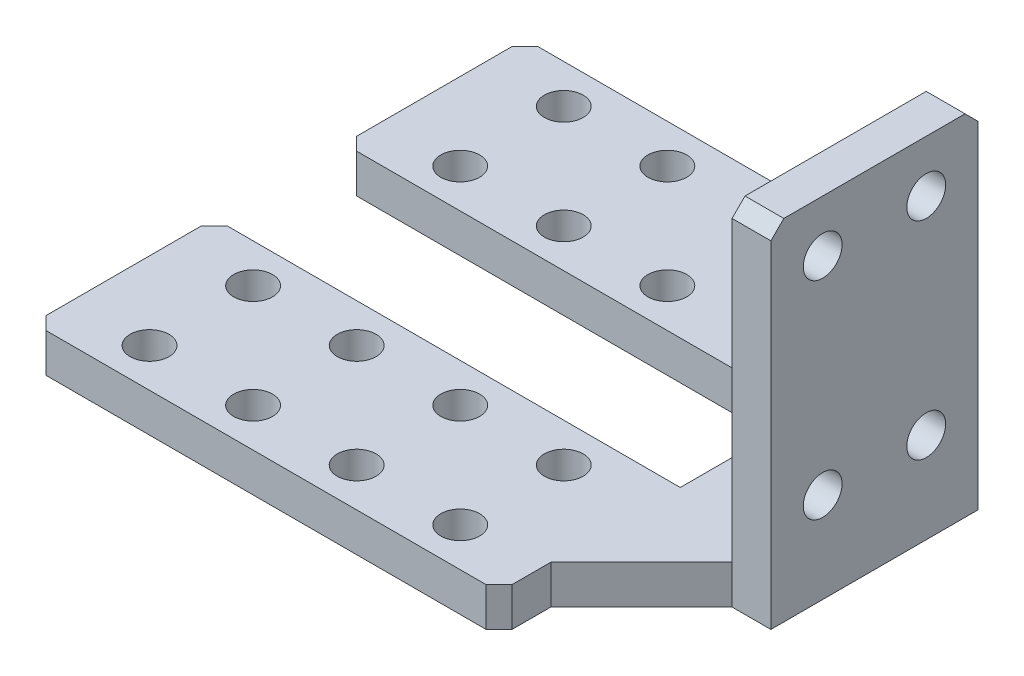
SolidWorks part; units mm, degrees
ref_plane "前视基准面" through (0, 0, 0) normal (0, 0, 1) x (1, 0, 0)
ref_plane "上视基准面" through (0, 0, 0) normal (0, 1, 0) x (1, 0, 0)
ref_plane "右视基准面" through (0, 0, 0) normal (1, 0, 0) x (0, 0, -1)
sketch "草图1" plane through (0, 0, 0) normal (0, 0, 1) x (1, 0, 0)
  line L1 (0, 0) -> (-3, 0)
  line L2 (0, 0) -> (0, 24)
  line L3 (0, 24) -> (-3, 24)
  line L4 (-3, 0) -> (-3, 24)
  dimension "D1" = 3
  dimension "D2" = 24
extrude "凸台-拉伸1" add sketch "草图1" along normal blind 16
sketch "草图2" plane through (-3, 0, 0) normal (-1, 0, 0) x (0, 0, 1)
  line L0 (16, 0) -> (0, 0) construction
  line L1 (16, 24) -> (16, 0) construction
  line L2 (0, 24) -> (0, 0) construction
  line L3 (4, -2.8728) -> (4, 29.3355) construction
  line L4 (12, -2.8728) -> (12, 30.8512) construction
  circle A0 centre (4, 4) radius 1.5
  circle A1 centre (12, 4) radius 1.5
  circle A2 centre (4, 20) radius 1.5
  circle A3 centre (12, 20) radius 1.5
  dimension "D1" = 4
  dimension "D2" = 4
  dimension "D3" = 3
  dimension "D4" = 4
  dimension "D5" = 4
  dimension "D6" = 3
  dimension "D7" = 16
  dimension "D8" = 16
  dimension "D9" = 3
  dimension "D10" = 3
extrude "切除-拉伸1" cut sketch "草图2" against normal blind 16
chamfer "倒角1" distance 1 angle 45 2 edges at (-1.5, 24, 16) (-1.5, 24, 0)
sketch "草图3" plane through (0, 0, 0) normal (1, 0, 0) x (0, 0, -1)
  line L0 (-16, 0) -> (-16, 23) construction
  line L1 (-16, 0) -> (0, 0)
  line L2 (-16, 0) -> (-16, -3)
  line L3 (-16, -3) -> (0, -3)
  line L4 (0, 0) -> (0, -3)
  line L5 (-16, 0) -> (0, 0) construction
  point P4 (-16, -1.5)
  dimension "D1" = 16
  dimension "D2" = 3
extrude "凸台-拉伸2" add sketch "草图3" against normal blind 10
sketch "草图4" plane through (0, 0, 0) normal (0, 1, 0) x (1, 0, 0)
  line L0 (-10, 0) -> (-10, -16) construction
  line L1 (-46, 11) -> (-10, 11)
  line L2 (-46, 11) -> (-46, -3)
  line L3 (-46, -27) -> (-10, -27)
  line L4 (-10, 11) -> (-10, -27)
  line L5 (-10, 0) -> (-3, 0) construction
  line L6 (-10, -16) -> (-3, -16) construction
  line L7 (-10, -8) -> (-54.8697, -8) construction
  line L8 (-10, -3) -> (-46, -3)
  line L9 (-10, -3) -> (-10, -13)
  line L10 (-10, -13) -> (-46, -13)
  line L12 (-46, -13) -> (-46, -27)
  line M10 (-10, 0) -> (-10, -16)
  dimension "D1" = 11
  dimension "D2" = 11
  dimension "D3" = 36
  dimension "D4" = 10
extrude "凸台-拉伸3" add sketch "草图4" against normal up to surface (3 mm away) contours L8 L4 L1 L2 M10 | L10 L12 L3 L4 M10 up to face at (-5, -3, 8)
chamfer "倒角2" distance 1 angle 45 6 edges at (-10, -1.5, 27) (-46, -1.5, 27) (-46, -1.5, 13) (-46, -1.5, 3) (-46, -1.5, -11) (-10, -1.5, -11)
sketch "草图5" plane through (0, 0, 0) normal (0, 1, 0) x (1, 0, 0)
  line L0 (-10, -8) -> (-46, -8) construction
  line L1 (-10, -3) -> (-10, -13) construction
  line L2 (-46, 10) -> (-46, -26) construction
  line L3 (-40, 11) -> (-40, -27) construction
  line L6 (-45, 11) -> (-11, 11) construction
  line L7 (-45, -27) -> (-11, -27) construction
  line L8 (-32, 11) -> (-32, -27) construction
  line L9 (-24, 11) -> (-24, -27) construction
  line L10 (-16, 11) -> (-16, -27) construction
  line L11 (-11.8804, 0) -> (-44.2696, 0) construction
  line L12 (-44.2696, -16) -> (-11.8804, -16) construction
  line L13 (-44.8105, 8) -> (-14.0442, 8) construction
  line L14 (-43.661, -24) -> (-12.7595, -24) construction
  circle A0 centre (-40, 8) radius 1.5
  circle A1 centre (-32, 8) radius 1.5
  circle A2 centre (-24, 8) radius 1.5
  circle A3 centre (-16, 8) radius 1.5
  circle A4 centre (-40, 0) radius 1.5
  circle A5 centre (-32, 0) radius 1.5
  circle A6 centre (-24, 0) radius 1.5
  circle A7 centre (-16, 0) radius 1.5
  circle A8 centre (-40, -16) radius 1.5
  circle A9 centre (-40, -24) radius 1.5
  circle A10 centre (-32, -16) radius 1.5
  circle A11 centre (-32, -24) radius 1.5
  circle A12 centre (-24, -16) radius 1.5
  circle A13 centre (-24, -24) radius 1.5
  circle A14 centre (-16, -16) radius 1.5
  circle A15 centre (-16, -24) radius 1.5
  dimension "D9" = 3
  dimension "D1" = 6
  dimension "D2" = 8
  dimension "D3" = 8
  dimension "D4" = 8
  dimension "D5" = 8
  dimension "D6" = 8
  dimension "D7" = 8
  dimension "D8" = 8
extrude "切除-拉伸2" cut sketch "草图5" against normal blind 10
chamfer "倒角3" distance 7 angle 45 2 edges at (-10, -1.5, 16) (-10, -1.5, 0)
